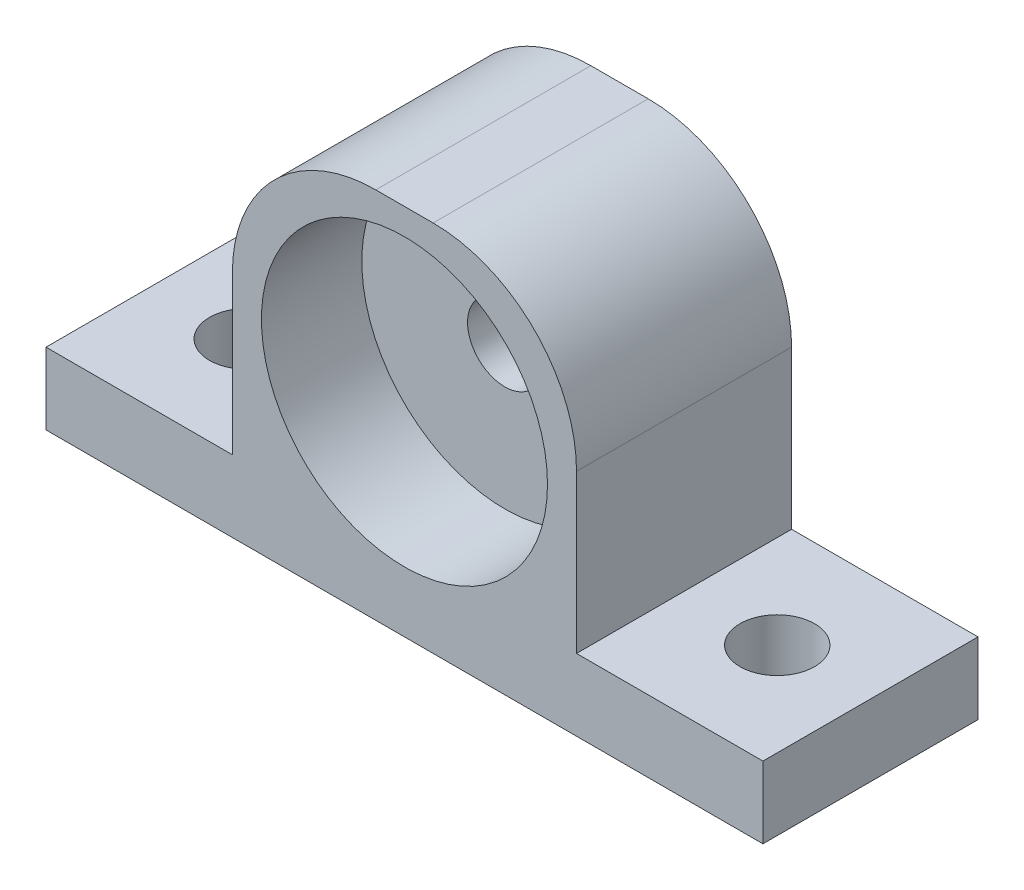
SolidWorks part; units mm, degrees
ref_plane "Front Plane" through (0, 0, 0) normal (0, 0, 1) x (1, 0, 0)
ref_plane "Top Plane" through (0, 0, 0) normal (0, 1, 0) x (1, 0, 0)
ref_plane "Right Plane" through (0, 0, 0) normal (1, 0, 0) x (0, 0, -1)
sketch "Sketch1" plane through (0, 0, 0) normal (0, 1, 0) x (1, 0, 0)
  line L1 (-62.2874, 13.8119) -> (1.2126, 13.8119)
  line L2 (-62.2874, 13.8119) -> (-62.2874, -5.2381)
  line L3 (-62.2874, -5.2381) -> (1.2126, -5.2381)
  line L4 (1.2126, 13.8119) -> (1.2126, -5.2381)
  dimension "D1" = 63.5
  dimension "D2" = 19.05
extrude "Boss-Extrude1" add sketch "Sketch1" along normal blind 6.35
sketch "Sketch2" plane through (0, 6.35, 0) normal (0, 1, 0) x (1, 0, 0)
  line L0 (1.2126, 13.8119) -> (-62.2874, 13.8119) construction
  line L1 (-45.7774, 13.8119) -> (-15.2974, 13.8119)
  line L2 (-45.7774, 13.8119) -> (-45.7774, -5.2381)
  line L3 (-45.7774, -5.2381) -> (-15.2974, -5.2381)
  line L4 (-15.2974, 13.8119) -> (-15.2974, -5.2381)
  line L5 (-62.2874, -5.2381) -> (1.2126, -5.2381) construction
  line L6 (-62.2874, 13.8119) -> (-62.2874, -5.2381) construction
  line L7 (1.2126, -5.2381) -> (1.2126, 13.8119) construction
  dimension "D1" = 16.51
  dimension "D2" = 16.51
extrude "Boss-Extrude2" add sketch "Sketch2" along normal blind 26.67
sketch "Sketch3" plane through (0, 6.35, 0) normal (0, 1, 0) x (1, 0, 0)
  line L0 (-45.7774, 13.8119) -> (-45.7774, -5.2381) construction
  line L1 (-15.2974, -5.2381) -> (-15.2974, 13.8119) construction
  line L2 (1.2126, 13.8119) -> (-15.2974, 13.8119) construction
  line L3 (-45.7774, 13.8119) -> (-62.2874, 13.8119) construction
  circle A0 centre (-54.0324, 4.2869) radius 3.302
  circle A1 centre (-7.0424, 4.2869) radius 3.302
  dimension "D1" = 6.604
  dimension "D2" = 6.604
  dimension "D3" = 8.255
  dimension "D4" = 8.255
  dimension "D5" = 9.525
  dimension "D6" = 9.525
extrude "Cut-Extrude1" cut sketch "Sketch3" against normal up to next
sketch "Sketch4" plane through (0, 0, 5.2381) normal (0, 0, 1) x (1, 0, 0)
  line L0 (-15.2974, 33.02) -> (-15.2974, 6.35) construction
  line L3 (-62.2874, 0) -> (1.2126, 0) construction
  circle A0 centre (-30.5374, 18.034) radius 12.6691
  point P6 (-102.4974, 38.2631)
  dimension "D1" = 15.24
  dimension "D2" = 18.034
extrude "Cut-Extrude2" cut sketch "Sketch4" against normal blind 8.89
sketch "Sketch5" plane through (0, 0, 5.2381) normal (0, 0, 1) x (1, 0, 0)
  line L0 (-62.2874, 0) -> (1.2126, 0) construction
  line L1 (-15.2974, 33.02) -> (-15.2974, 6.35) construction
  circle A0 centre (-30.5374, 18.034) radius 3.302
  point P2 (-30.5374, 0)
  point P7 (-87.8681, 24.8146)
  dimension "D3" = 6.604
  dimension "D1" = 18.034
  dimension "D2" = 15.24
extrude "Cut-Extrude3" cut sketch "Sketch5" against normal through all
fillet "Fillet1" radius 12.7 2 edges at (-45.7774, 33.02, -4.2869) (-15.2974, 33.02, -4.2869)
